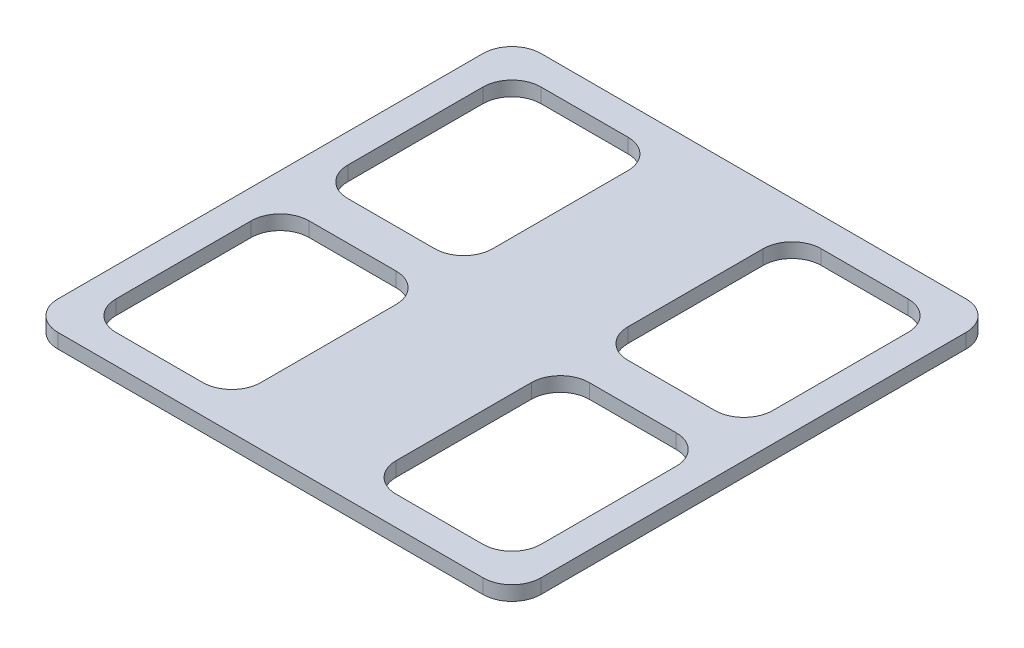
SolidWorks part; units mm, degrees
ref_plane "前视基准面" through (0, 0, 0) normal (0, 0, 1) x (1, 0, 0)
ref_plane "上视基准面" through (0, 0, 0) normal (0, 1, 0) x (1, 0, 0)
ref_plane "右视基准面" through (0, 0, 0) normal (1, 0, 0) x (0, 0, -1)
sketch "草图1" plane through (0, 0, 0) normal (0, 1, 0) x (1, 0, 0)
  line L0 (70, 120) -> (220, 120) construction
  line L1 (220, 250) -> (-220, 250)
  line L2 (250, 220) -> (250, -220)
  line L3 (220, -250) -> (-220, -250)
  line L4 (-250, 220) -> (-250, -220)
  line L5 (0, -250) -> (0, 250) construction
  line L6 (250, 0) -> (-250, 0) construction
  line L7 (-100, 20) -> (-190, 20)
  line L8 (-70, 50) -> (-70, 190)
  line L9 (-100, 220) -> (-190, 220)
  line L10 (-220, 50) -> (-220, 190)
  line L11 (-145, 220) -> (-145, 20) construction
  line L12 (-70, 120) -> (-220, 120) construction
  line L13 (145, 220) -> (145, 20) construction
  line L14 (220, 50) -> (220, 190)
  line L15 (100, 220) -> (190, 220)
  line L16 (70, 50) -> (70, 190)
  line L17 (100, 20) -> (190, 20)
  line L18 (-70, -120) -> (-220, -120) construction
  line L19 (-145, -220) -> (-145, -20) construction
  line L20 (-220, -50) -> (-220, -190)
  line L21 (-100, -220) -> (-190, -220)
  line L22 (-70, -50) -> (-70, -190)
  line L23 (-100, -20) -> (-190, -20)
  line L24 (145, -220) -> (145, -20) construction
  line L25 (70, -120) -> (220, -120) construction
  line L26 (100, -20) -> (190, -20)
  line L27 (70, -50) -> (70, -190)
  line L28 (100, -220) -> (190, -220)
  line L29 (220, -50) -> (220, -190)
  arc A0 (190, -20) -> (220, -50) centre (190, -50) cw
  arc A1 (190, -220) -> (220, -190) centre (190, -190) ccw
  arc A2 (70, -190) -> (100, -220) centre (100, -190) ccw
  arc A3 (100, -20) -> (70, -50) centre (100, -50) ccw
  arc A4 (70, 50) -> (100, 20) centre (100, 50) ccw
  arc A5 (220, 50) -> (190, 20) centre (190, 50) cw
  arc A6 (220, 190) -> (190, 220) centre (190, 190) ccw
  arc A7 (100, 220) -> (70, 190) centre (100, 190) ccw
  arc A8 (-190, 20) -> (-220, 50) centre (-190, 50) cw
  arc A9 (-190, 220) -> (-220, 190) centre (-190, 190) ccw
  arc A10 (-70, 190) -> (-100, 220) centre (-100, 190) ccw
  arc A11 (-100, 20) -> (-70, 50) centre (-100, 50) ccw
  arc A12 (-100, -220) -> (-70, -190) centre (-100, -190) ccw
  arc A13 (-70, -50) -> (-100, -20) centre (-100, -50) ccw
  arc A14 (-220, -50) -> (-190, -20) centre (-190, -50) cw
  arc A15 (-220, -190) -> (-190, -220) centre (-190, -190) ccw
  arc A16 (-220, -250) -> (-250, -220) centre (-220, -220) cw
  arc A17 (250, -220) -> (220, -250) centre (220, -220) cw
  arc A18 (220, 250) -> (250, 220) centre (220, 220) cw
  arc A19 (-220, 250) -> (-250, 220) centre (-220, 220) ccw
  point P0 (0, 0)
  point P4 (-145, 120)
  point P17 (145, 120)
  point P26 (-145, -120)
  point P35 (145, -120)
  point P38 (220, -20)
  point P41 (220, -220)
  point P44 (70, -220)
  point P47 (70, -20)
  point P50 (70, 20)
  point P53 (220, 20)
  point P56 (220, 220)
  point P59 (70, 220)
  point P62 (-220, 20)
  point P66 (-220, 220)
  point P69 (-70, 220)
  point P72 (-70, 20)
  point P75 (-70, -220)
  point P78 (-70, -20)
  point P81 (-220, -20)
  point P84 (-220, -220)
  point P87 (-250, -250)
  point P92 (250, 250)
  point P95 (-250, 250)
  dimension "D7" = 30
  dimension "D1" = 500
  dimension "D2" = 500
  dimension "D3" = 200
  dimension "D4" = 150
  dimension "D5" = 30
  dimension "D6" = 30
extrude "凸台-拉伸1" add sketch "草图1" along normal blind 15
